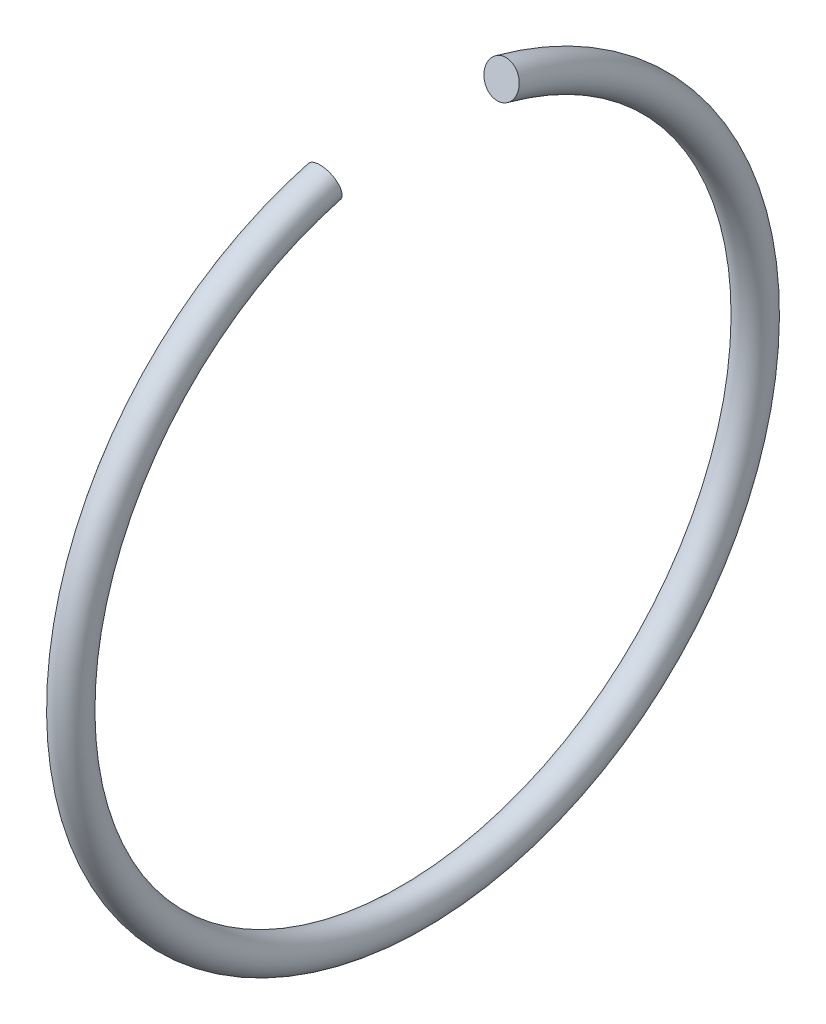
SolidWorks part; units mm, degrees
ref_plane "Přední rovina" through (0, 0, 0) normal (0, 0, 1) x (1, 0, 0)
ref_plane "Horní rovina" through (0, 0, 0) normal (0, 1, 0) x (1, 0, 0)
ref_plane "Pravá rovina" through (0, 0, 0) normal (1, 0, 0) x (0, 0, -1)
sketch "Skica1" plane through (0, 0, 0) normal (0, 0, 1) x (1, 0, 0)
  line L0 (-67.4823, 0) -> (-363.0393, 0) construction
  line L1 (-67.4823, 0) -> (-363.0393, 0) construction
  circle A0 centre (-213.8, -25) radius 1.25 construction
  circle A1 centre (-213.8, -25) radius 1.25
revolve "Rotovat1" add sketch "Skica1" angle 330 mid plane about L1
